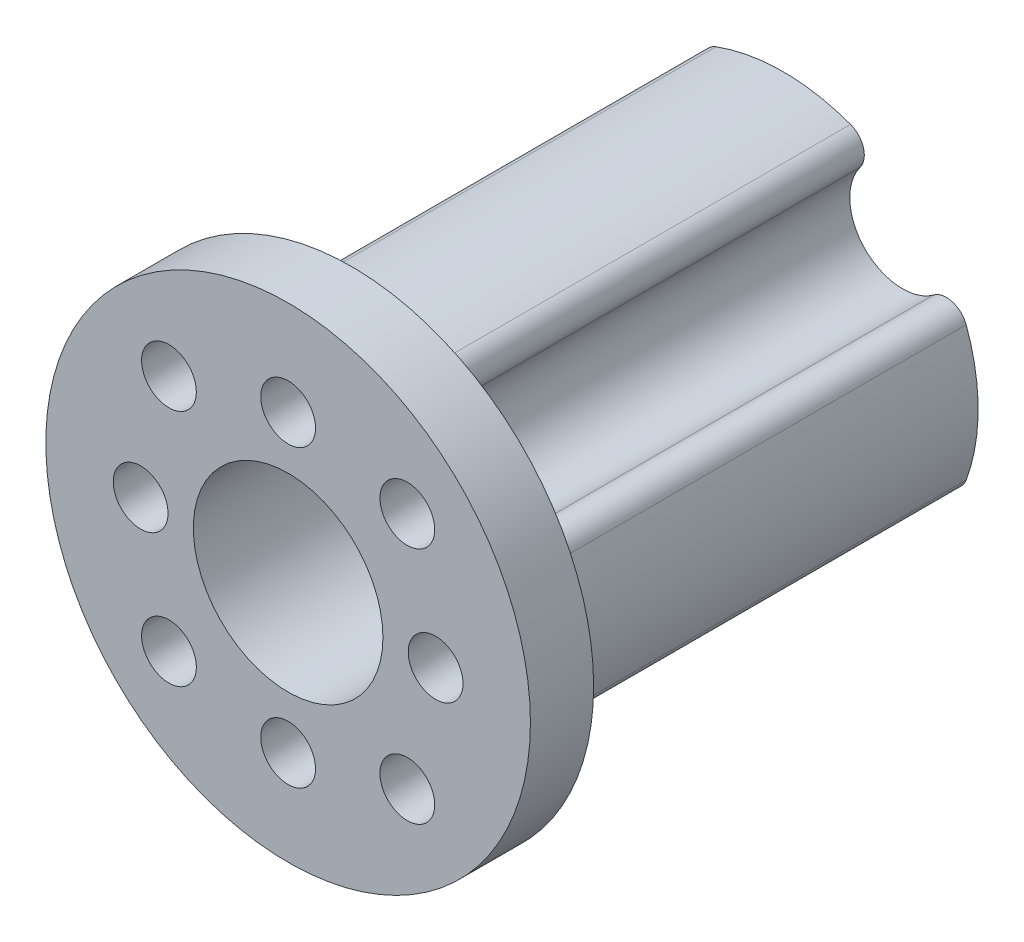
SolidWorks part; units mm, degrees
ref_plane "Plan de face" through (0, 0, 0) normal (0, 0, 1) x (1, 0, 0)
ref_plane "Plan de dessus" through (0, 0, 0) normal (0, 1, 0) x (1, 0, 0)
ref_plane "Plan de droite" through (0, 0, 0) normal (1, 0, 0) x (0, 0, -1)
sketch "Esquisse1" plane through (0, 0, 0) normal (0, 0, 1) x (1, 0, 0)
  circle A0 centre (0, 0) radius 9.25
  dimension "D1" = 18.5
extrude "Boss.-Extru.1" add sketch "Esquisse1" along normal blind 23.5
sketch "Esquisse2" plane through (0, 0, 23.5) normal (0, 0, 1) x (1, 0, 0)
  line L0 (0, 0) -> (7, 0) construction
  circle A0 centre (7, 0) radius 1.3
  circle A1 centre (0, -7) radius 1.3
  circle A2 centre (-7, 0) radius 1.3
  circle A3 centre (0, 7) radius 1.3
  point P13 (0, 0)
  dimension "D1" = 2.6
  dimension "D2" = 7
  dimension "D3" = 4
extrude "Enlèv. mat.-Extru.1" cut sketch "Esquisse2" against normal through all both and the other way through all
sketch "Esquisse3" plane through (0, 0, 23.5) normal (0, 0, 1) x (1, 0, 0)
  circle A1 centre (0, 0) radius 4.5
  dimension "D1" = 9
extrude "Enlèv. mat.-Extru.2" cut sketch "Esquisse3" against normal through all both and the other way through all
sketch "Esquisse4" plane through (0, 0, 23.5) normal (0, 0, 1) x (1, 0, 0)
  circle A0 centre (0, 0) radius 9.25
  circle A1 centre (0, 0) radius 11.5
  circle A2 centre (0, 0) radius 9.25 construction
  dimension "D1" = 23
extrude "Boss.-Extru.2" add sketch "Esquisse4" against normal blind 3
sketch "Esquisse5" plane through (0, 0, 23.5) normal (0, 0, 1) x (1, 0, 0)
  line L0 (5.6569, 5.6569) -> (0, 0) construction
  line L1 (0, 0) -> (2.5725, 0) construction
  circle A0 centre (5.6569, 5.6569) radius 2.5
  circle A1 centre (5.6569, -5.6569) radius 2.5
  circle A2 centre (-5.6569, -5.6569) radius 2.5
  circle A3 centre (-5.6569, 5.6569) radius 2.5
  point P13 (0, 0)
  point P14 (0, 0)
  dimension "D3" = 5
  dimension "D1" = 45
  dimension "D2" = 8
  dimension "D4" = 4
extrude "Enlèv. mat.-Extru.3" cut sketch "Esquisse5" against normal through all both and the other way through all
sketch "Esquisse6" plane through (0, 0, 23.5) normal (0, 0, 1) x (1, 0, 0)
  circle A0 centre (-5.6569, 5.6569) radius 2.5
  circle A1 centre (-5.6569, 5.6569) radius 1.3
  circle A2 centre (-5.6569, 5.6569) radius 2.5 construction
  circle A3 centre (5.6569, 5.6569) radius 2.5
  circle A4 centre (5.6569, 5.6569) radius 1.3
  circle A5 centre (5.6569, -5.6569) radius 2.5
  circle A6 centre (5.6569, -5.6569) radius 1.3
  circle A7 centre (-5.6569, -5.6569) radius 2.5
  circle A8 centre (-5.6569, -5.6569) radius 1.3
  point P18 (0, 0)
  dimension "D1" = 2.6
  dimension "D2" = 4
extrude "Boss.-Extru.3" add sketch "Esquisse6" against normal up to vertex
fillet "Congé1" radius 1 8 edges at (4.7005, -7.9667, 10.25) (7.9667, -4.7005, 10.25) (-7.9667, -4.7005, 10.25) (-4.7005, -7.9667, 10.25) (-4.7005, 7.9667, 10.25) (-7.9667, 4.7005, 10.25) (7.9667, 4.7005, 10.25) (4.7005, 7.9667, 10.25)
